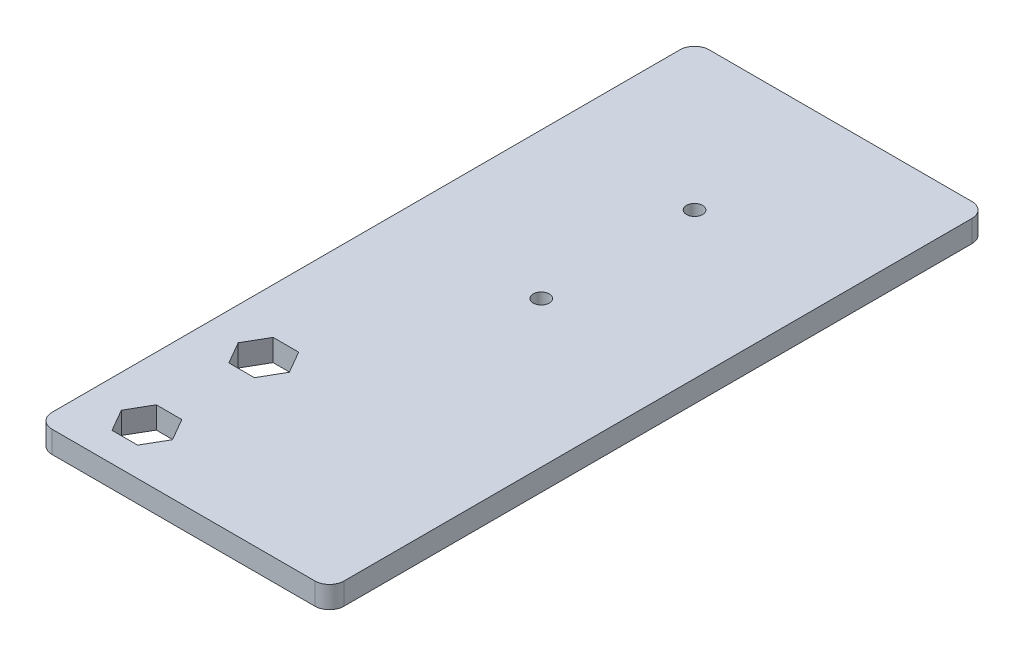
SolidWorks part; units mm, degrees
ref_plane "Plan de face" through (0, 0, 0) normal (0, 0, 1) x (1, 0, 0)
ref_plane "Plan de dessus" through (0, 0, 0) normal (0, 1, 0) x (1, 0, 0)
ref_plane "Plan de droite" through (0, 0, 0) normal (1, 0, 0) x (0, 0, -1)
sketch "Esquisse1" plane through (0, 0, 0) normal (0, 1, 0) x (1, 0, 0)
  line L5 (13, 2) -> (13, 88)
  line L7 (15, 0) -> (51, 0)
  line L8 (53, 88) -> (53, 2)
  line L11 (15, 90) -> (51, 90)
  arc A0 (51, 90) -> (53, 88) centre (51, 88) cw
  arc A1 (15, 0) -> (13, 2) centre (15, 2) cw
  arc A2 (51, 0) -> (53, 2) centre (51, 2) ccw
  arc A3 (15, 90) -> (13, 88) centre (15, 88) ccw
  point P12 (53, 90)
  point P15 (13, 0)
  point P26 (13, 90)
  dimension "D3" = 2
  dimension "D5" = 2
  dimension "D1" = 90
  dimension "D2" = 40
  dimension "D4" = 13
extrude "Extrusion1" add sketch "Esquisse1" along normal blind 3
sketch "Esquisse2" plane through (0, 0, 0) normal (0, -1, 0) x (1, 0, 0)
  line L0 (13, -88) -> (13, -2) construction
  line L1 (15, 0) -> (51, 0) construction
  circle A14 centre (21, -7) radius 1.1
  circle A15 centre (21, -23) radius 1.1
  dimension "D4" = 2.2
  dimension "D5" = 2.2
  dimension "D1" = 8
  dimension "D2" = 16
  dimension "D3" = 7
extrude "Enlèv. mat.-Extru.1" cut sketch "Esquisse2" against normal through all
sketch "Esquisse3" plane through (0, 3, 0) normal (0, 1, 0) x (1, 0, 0)
  line L0 (15, 0) -> (51, 0) construction
  line L1 (17.5, 23) -> (19.25, 19.9689)
  line L2 (19.25, 19.9689) -> (22.75, 19.9689)
  line L3 (22.75, 19.9689) -> (24.5, 23)
  line L4 (24.5, 23) -> (22.75, 26.0311)
  line L5 (22.75, 26.0311) -> (19.25, 26.0311)
  line L6 (19.25, 26.0311) -> (17.5, 23)
  line L7 (17.5, 7) -> (19.25, 3.9689)
  line L8 (19.25, 3.9689) -> (22.75, 3.9689)
  line L9 (22.75, 3.9689) -> (24.5, 7)
  line L10 (24.5, 7) -> (22.75, 10.0311)
  line L11 (22.75, 10.0311) -> (19.25, 10.0311)
  line L12 (19.25, 10.0311) -> (17.5, 7)
  line L13 (13, 88) -> (13, 2) construction
  line L15 (51, 90) -> (15, 90) construction
  circle A0 centre (21, 23) radius 3.0311 construction
  circle A1 centre (21, 7) radius 3.0311 construction
  circle A2 centre (33, 70) radius 1.1
  circle A3 centre (33, 49) radius 1.1
  dimension "D6" = 2.2
  dimension "D1" = 3.5
  dimension "D2" = 3.5
  dimension "D3" = 20
  dimension "D4" = 20
  dimension "D5" = 21
extrude "Enlèv. mat.-Extru.2" cut sketch "Esquisse3" against normal through all
